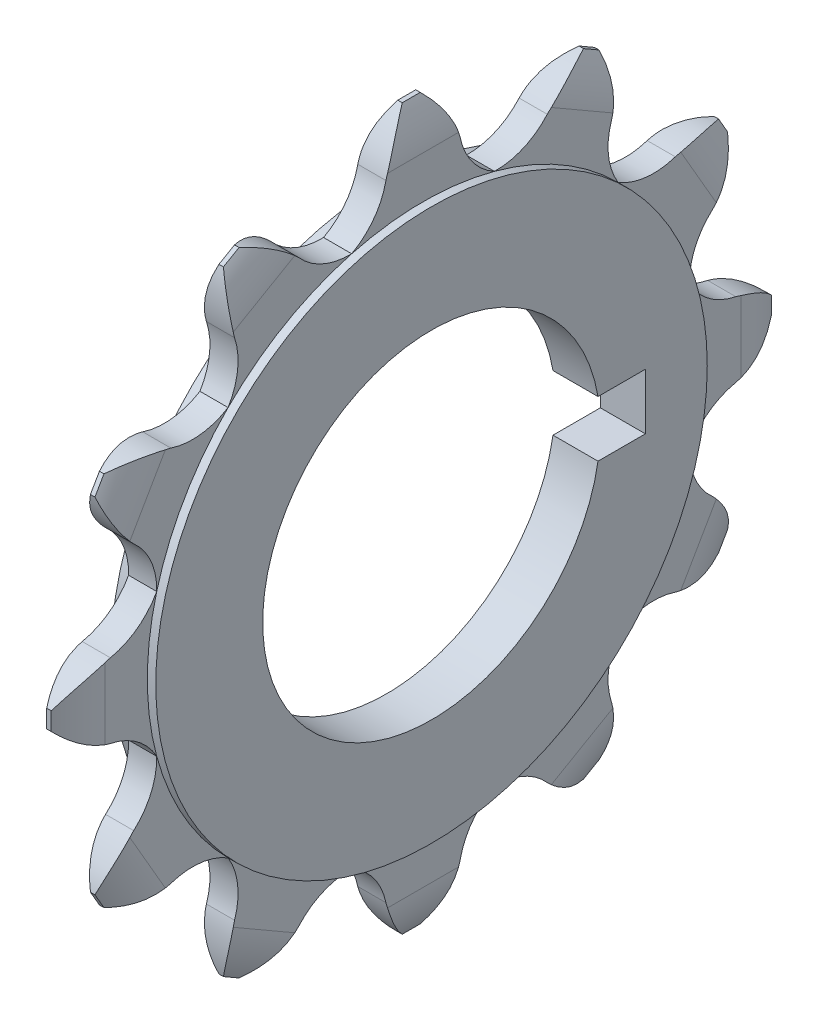
SolidWorks part; units mm, degrees
material "1060 Alloy"
ref_plane "Front Plane" through (0, 0, 0) normal (0, 0, 1) x (1, 0, 0)
ref_plane "Top Plane" through (0, 0, 0) normal (0, 1, 0) x (1, 0, 0)
ref_plane "Right Plane" through (0, 0, 0) normal (1, 0, 0) x (0, 0, -1)
sketch "Sketch1" plane through (0, 0, 0) normal (1, 0, 0) x (0, 0, -1)
  line L1 (52.0456, 52.0456) -> (19.05, 71.0956)
  line L2 (19.05, 71.0956) -> (-19.05, 71.0956)
  line L3 (-19.05, 71.0956) -> (-52.0456, 52.0456)
  line L4 (-52.0456, 52.0456) -> (-71.0956, 19.05)
  line L5 (-71.0956, 19.05) -> (-71.0956, -19.05)
  line L6 (-71.0956, -19.05) -> (-52.0456, -52.0456)
  line L7 (-52.0456, -52.0456) -> (-19.05, -71.0956)
  line L8 (-19.05, -71.0956) -> (19.05, -71.0956)
  line L9 (19.05, -71.0956) -> (52.0456, -52.0456)
  line L10 (52.0456, -52.0456) -> (71.0956, -19.05)
  line L11 (71.0956, -19.05) -> (71.0956, 19.05)
  line L12 (71.0956, 19.05) -> (52.0456, 52.0456)
  circle A0 centre (0, 0) radius 71.0956 construction
  circle A1 centre (0, 0) radius 62.23 construction
  point P1 (0, 71.0956)
  point P27 (0, 0)
  point P28 (0, 0)
  point P29 (0, 0)
  point P30 (0, 0)
  dimension "D2" = 124.46
  dimension "D1" = 38.1
sketch "Sketch2" plane through (0, 0, 0) normal (1, 0, 0) x (0, 0, -1)
  line L0 (-19.05, 71.0956) -> (19.05, 71.0956) construction
  arc A8 (-15.875, 80.7467) -> (15.875, 80.7467) centre (0, 129.0026) ccw
  arc A9 (-15.875, 61.4444) -> (15.875, 61.4444) centre (0, 13.1886) cw
  circle A12 centre (-19.05, 71.0956) radius 5.588
  circle A13 centre (19.05, 71.0956) radius 5.588
  circle A14 centre (-19.05, 71.0956) radius 10.16
  circle A15 centre (19.05, 71.0956) radius 10.16
  point P11 (0, 0)
  point P13 (0, 0)
  point P14 (0, 0)
  point P15 (0, 0)
  dimension "D1" = 11.176
  dimension "D2" = 20.32
  dimension "D3" = 50.8
  dimension "D4" = 50.8
sketch "Sketch3" plane through (0, 0, 0) normal (1, 0, 0) x (0, 0, -1)
  line L0 (0, 0) -> (-19.05, 71.0956) construction
  line L1 (0, 0) -> (0, 71.0956) construction
  line L2 (19.05, 71.0956) -> (-19.05, 71.0956) construction
  line L3 (0, 71.0956) -> (0, 81.2556) construction
  line L4 (-5.08, 81.2556) -> (5.08, 81.2556) construction
  line L5 (-5.08, 81.2556) -> (-11.43, 61.1713) construction
  line L6 (5.08, 81.2556) -> (11.43, 61.1713) construction
  circle A1 centre (0, 0) radius 62.23 construction
  arc A2 (-2.032, 81.2556) -> (-8.382, 70.5693) centre (14.2282, 64.3636) ccw
  arc A3 (-8.382, 70.5693) -> (-16.1063, 60.1096) centre (-23.4807, 73.6374) cw
  point P11 (0, 81.2556)
  point P20 (0, 0)
  point P21 (0, 0)
  point P22 (-7.3648, 69.2425)
  dimension "D1" = 10.16
  dimension "D2" = 10.16
  dimension "D3" = 22.86
  dimension "D4" = 2.032
  dimension "D5" = 9.398
  dimension "D6" = 8.382
sketch "Sketch4" plane through (0, 0, 0) normal (1, 0, 0) x (0, 0, -1)
  line L0 (0, 0) -> (0, -16.2704) construction
  line L1 (-2.032, 81.2556) -> (2.032, 81.2556)
  arc A0 (-16.1063, 60.1096) -> (-8.382, 70.5693) centre (-23.4807, 73.6374) ccw construction
  arc A1 (-2.032, 81.2556) -> (-8.382, 70.5693) centre (14.2282, 64.3636) ccw construction
  arc A2 (-16.1063, 60.1096) -> (-8.382, 70.5693) centre (-23.4807, 73.6374) ccw
  arc A3 (-2.032, 81.2556) -> (-8.382, 70.5693) centre (14.2282, 64.3636) ccw
  arc A4 (16.1063, 60.1096) -> (8.382, 70.5693) centre (23.4807, 73.6374) cw
  arc A5 (2.032, 81.2556) -> (8.382, 70.5693) centre (-14.2282, 64.3636) cw
  arc A6 (-16.1063, 60.1096) -> (16.1063, 60.1096) centre (0, 0) cw
extrude "Boss-Extrude1" add sketch "Sketch4" along normal mid plane 6.35
sketch "Sketch5" plane through (0, 0, 0) normal (0, 0, 1) x (1, 0, 0)
  line L0 (3.175, 81.2556) -> (-3.175, 81.2556) construction
  line L1 (0, 70.5693) -> (0, 65.6969) construction
  line L2 (3.175, 70.5693) -> (-3.175, 70.5693) construction
  line L3 (0, 52.0456) -> (0, 71.0956) construction
  line L4 (0, 60.9356) -> (0, 81.2556) construction
  line L5 (-0.508, 81.2556) -> (0.508, 81.2556)
  line L6 (-3.175, 70.5693) -> (-20.3218, 70.5693)
  line L7 (-20.3218, 70.5693) -> (-20.3218, 94.4901)
  line L8 (-20.3218, 94.4901) -> (13.239, 94.4901)
  line L9 (13.239, 94.4901) -> (13.239, 70.5693)
  line L10 (13.239, 70.5693) -> (3.175, 70.5693)
  arc A0 (-0.508, 81.2556) -> (-3.175, 70.5693) centre (17.1359, 71.1762) ccw
  arc A1 (0.508, 81.2556) -> (3.175, 70.5693) centre (-17.1359, 71.1762) cw
  dimension "D2" = 20.32
  dimension "D1" = 0.508
extrude "Cut-Extrude1" cut sketch "Sketch5" against normal through all both and the other way through all
pattern_circular "CirPattern1" count 12 over 360 about axis through (0, 0, 0) along (1, 0, 0) of bodies 120
sketch "Sketch6" plane through (0, 0, 0) normal (1, 0, 0) x (0, 0, -1)
  circle A0 centre (0, 0) radius 62.23 construction
  circle A1 centre (0, 0) radius 62.23
  circle A2 centre (0, 0) radius 38.1
  dimension "D1" = 76.2
extrude "Boss-Extrude2" add sketch "Sketch6" along normal mid plane 10.16
sketch "Sketch7" plane through (0, 0, 0) normal (1, 0, 0) x (0, 0, -1)
  line L1 (27.94, -6.311) -> (48.26, -6.311)
  line L2 (27.94, -6.311) -> (27.94, 6.311)
  line L3 (27.94, 6.311) -> (48.26, 6.311)
  line L4 (48.26, -6.311) -> (48.26, 6.311)
  line L5 (27.94, -6.311) -> (48.26, 6.311) construction
  line L6 (27.94, 6.311) -> (48.26, -6.311) construction
  circle A0 centre (0, 0) radius 38.1 construction
  point P0 (38.1, 0)
  dimension "D1" = 20.32
  dimension "D2" = 12.6219
extrude "Cut-Extrude2" cut sketch "Sketch7" against normal through all both and the other way through all
